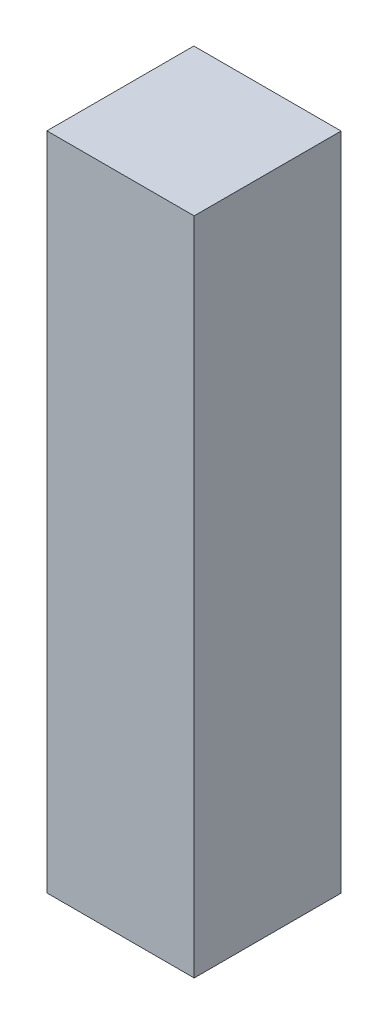
SolidWorks part; units mm, degrees
material "Balsa"
ref_plane "Front Plane" through (0, 0, 0) normal (0, 0, 1) x (1, 0, 0)
ref_plane "Top Plane" through (0, 0, 0) normal (0, 1, 0) x (1, 0, 0)
ref_plane "Right Plane" through (0, 0, 0) normal (1, 0, 0) x (0, 0, -1)
sketch "Sketch2" plane through (0, 0, 0) normal (0, 1, 0) x (1, 0, 0)
  line L1 (19.1911, 17.7372) -> (223.2036, 17.7372)
  line L2 (19.1911, 17.7372) -> (19.1911, -185.8103)
  line L3 (19.1911, -185.8103) -> (223.2036, -185.8103)
  line L4 (223.2036, 17.7372) -> (223.2036, -185.8103)
extrude "Boss-Extrude1" add sketch "Sketch2" against normal blind 914.4
